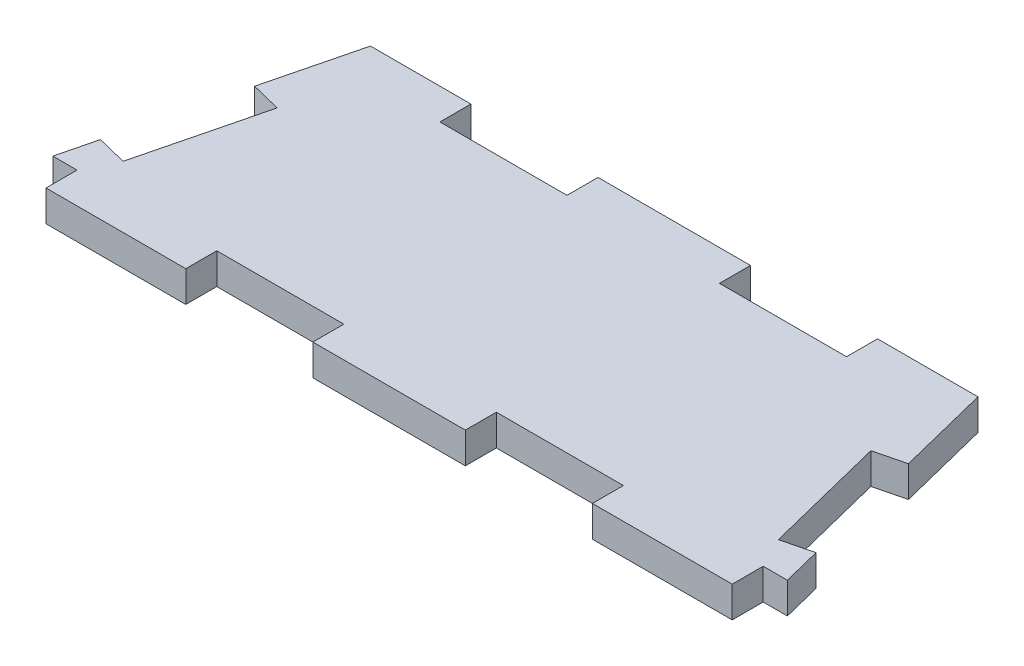
SolidWorks part; units mm, degrees
ref_plane "Alzado" through (0, 0, 0) normal (0, 0, 1) x (1, 0, 0)
ref_plane "Planta" through (0, 0, 0) normal (0, 1, 0) x (1, 0, 0)
ref_plane "Vista lateral" through (0, 0, 0) normal (1, 0, 0) x (0, 0, -1)
sketch "Croquis1" plane through (0, 0, 0) normal (0, 1, 0) x (1, 0, 0)
  line L0 (-27, 0) -> (-16, 0)
  line L1 (0, 0) -> (0, 20) construction
  line L2 (-22, 20) -> (22, 20) construction
  line L3 (-27, 0) -> (-22, 20) construction
  line L4 (27, 0) -> (22, 20) construction
  line L5 (-28.9051, 2.44) -> (-28.1545, 5.4425)
  line L6 (-23.9051, 22.44) -> (-16, 22.44)
  line L7 (28.9051, 2.44) -> (28.1545, 5.4425)
  line L8 (-27, 0) -> (-27, 2.44)
  line L9 (27, 0) -> (27, 2.44)
  line L10 (-29.3671, 0.5918) -> (-23.9051, 22.44) construction
  line L11 (29.3671, 0.5918) -> (23.9051, 22.44) construction
  line L12 (-27, 2.44) -> (-28.9051, 2.44)
  line L13 (27, 2.44) -> (28.9051, 2.44)
  line L14 (28.9051, 2.44) -> (29.5151, 0) construction
  line L15 (16, 22.44) -> (23.9051, 22.44)
  line L16 (-16, 22.44) -> (-16, 20)
  line L17 (-16, 20) -> (-6, 20)
  line L18 (-6, 22.44) -> (-6, 20)
  line L19 (25.7291, 15.1439) -> (23.9051, 22.44)
  line L20 (6, 22.44) -> (6, 20)
  line L21 (6, 20) -> (16, 20)
  line L22 (16, 22.44) -> (16, 20)
  line L23 (29.5151, 0) -> (27, 0) construction
  line L24 (-28.9051, 2.44) -> (-29.5151, 0) construction
  line L25 (-29.5151, 0) -> (-27, 0) construction
  line L26 (25.7873, 4.8507) -> (23.362, 14.5521)
  line L27 (25.7873, 4.8507) -> (28.1545, 5.4425)
  line L28 (23.362, 14.5521) -> (25.7291, 15.1439)
  line L29 (-6, 0) -> (6, 0)
  line L30 (-23.362, 14.5521) -> (-25.7873, 4.8507)
  line L31 (-23.362, 14.5521) -> (-25.7291, 15.1439)
  line L32 (-25.7873, 4.8507) -> (-28.1545, 5.4425)
  line L33 (-6, 22.44) -> (6, 22.44)
  line L34 (-25.7291, 15.1439) -> (-23.9051, 22.44)
  line L35 (-23.9051, 22.44) -> (23.9051, 22.44) construction
  line L36 (16, 0) -> (27, 0)
  line L37 (-6, 0) -> (-6, 2.44)
  line L38 (-6, 2.44) -> (-16, 2.44)
  line L39 (-16, 0) -> (-16, 2.44)
  line L41 (6, 0) -> (6, 2.44)
  line L42 (6, 2.44) -> (16, 2.44)
  line L43 (16, 0) -> (16, 2.44)
  point P3 (0, 0)
  point P8 (0, 20)
  point P43 (-56.4814, 21.9482)
  dimension "D2" = 20
  dimension "D3" = 44
  dimension "D5" = 2.44
  dimension "D6" = 2.44
  dimension "D7" = 6
  dimension "D8" = 10
  dimension "D9" = 6
  dimension "D10" = 10
  dimension "D11" = 5
  dimension "D12" = 10
  dimension "D13" = 2.44
  dimension "D14" = 5
  dimension "D15" = 10
  dimension "D16" = 2.44
  dimension "D17" = 6
  dimension "D18" = 10
  dimension "D19" = 10
  dimension "D20" = 6
  dimension "D21" = 2.44
  dimension "D22" = 2.44
  dimension "D4" = 2.44
extrude "Saliente-Extruir3" add sketch "Croquis1" along normal blind 2.44
